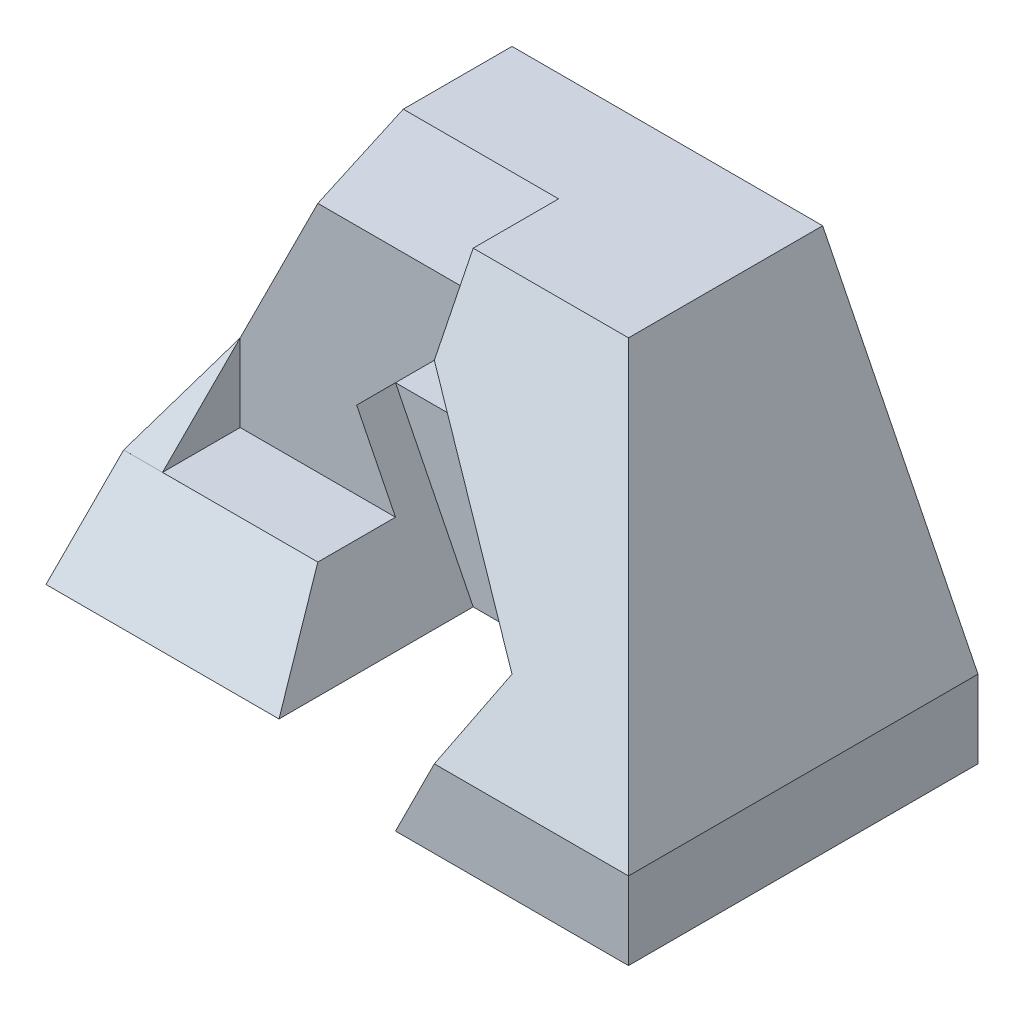
SolidWorks part; units mm, degrees
ref_plane "Front Plane" through (0, 0, 0) normal (0, 0, 1) x (1, 0, 0)
ref_plane "Top Plane" through (0, 0, 0) normal (0, 1, 0) x (1, 0, 0)
ref_plane "Right Plane" through (0, 0, 0) normal (1, 0, 0) x (0, 0, -1)
sketch "Sketch1" plane through (0, 0, 0) normal (0, 0, 1) x (1, 0, 0)
  line L0 (0, 0) -> (0, 20)
  line L1 (0, 20) -> (40, 100)
  line L2 (40, 100) -> (120, 100)
  line L3 (120, 100) -> (160, 20)
  line L4 (160, 20) -> (160, 0)
  line L5 (160, 0) -> (0, 0)
  dimension "D1" = 160
  dimension "D2" = 20
  dimension "D3" = 20
  dimension "D4" = 80
  dimension "D5" = 40
  dimension "D6" = 40
extrude "Boss-Extrude1" add sketch "Sketch1" along normal blind 90
sketch "Sketch2" plane through (0, 0, 0) normal (1, 0, 0) x (0, 0, -1)
  line L0 (0, 100) -> (-50, 100)
  line L1 (-50, 100) -> (-90, 20)
  line L2 (-90, 20) -> (-90, 0)
  line L3 (-90, 0) -> (0, 0)
  line L4 (0, 0) -> (0, 100)
  line L5 (-90, 20) -> (-90, 100)
  line L6 (-90, 100) -> (-50, 100)
  dimension "D1" = 50
  dimension "D2" = 0
extrude "Cut-Extrude1" cut sketch "Sketch2" along normal blind 251 contours L6 L5 L1
ref_plane "Plane1" through (0, 0, 90) normal (0, 0, 1) x (1, 0, 0)
sketch "Sketch7" plane through (0, 0, 90) normal (0, 0, 1) x (1, 0, 0)
  line L0 (60, 0) -> (100, 0)
  line L1 (0, 0) -> (160, 0) construction
  line L2 (100, 0) -> (120, 40)
  line L3 (120, 40) -> (80, 80)
  line L4 (80, 80) -> (40, 40)
  line L5 (40, 40) -> (60, 0)
  dimension "D1" = 40
  dimension "D2" = 60
  dimension "D3" = 20
  dimension "D4" = 20
  dimension "D5" = 40
  dimension "D6" = 40
  dimension "D7" = 20
  dimension "D8" = 40
extrude "Cut-Extrude7" cut sketch "Sketch7" against normal blind 40
sketch "Sketch8" plane through (0, 0, 50) normal (0, 0, 1) x (1, 0, 0)
  line L0 (40, 40) -> (120, 40)
  line L1 (120, 40) -> (80, 80)
  line L2 (80, 80) -> (40, 40)
extrude "Cut-Extrude8" cut sketch "Sketch8" against normal blind 20
sketch "Sketch9" plane through (0, 0, 0) normal (0, 1, 0) x (1, 0, 0)
  line L0 (160, -90) -> (110, -90) construction
  line L1 (40, -80) -> (110, -80)
  line L2 (40, -80) -> (40, -90)
  line L3 (40, -90) -> (110, -90)
  line L4 (110, -80) -> (110, -90)
  dimension "D1" = 10
  dimension "D2" = 70
  dimension "D3" = 50
  dimension "D4" = 0
extrude "Cut-Extrude9" cut sketch "Sketch9" along normal blind 190
sketch "Sketch10" plane through (0, 0, 0) normal (0, -1, 0) x (-1, 0, 0)
  line L0 (0, -90) -> (0, 0) construction
  line L1 (0, -90) -> (-39.999, -90)
  line L2 (0, -90) -> (0, -60.001)
  line L3 (0, -60.001) -> (-39.999, -60.001)
  line L4 (-39.999, -90) -> (-39.999, -60.001)
  line L5 (0, -90) -> (-40, -90) construction
  dimension "D1" = 39.999
  dimension "D2" = 29.999
extrude "Cut-Extrude13" cut sketch "Sketch10" against normal blind 190
sketch "Sketch11" plane through (40, 0, 0) normal (1, 0, 0) x (0, 0, -1)
  line L0 (-80, 40) -> (-80, 0)
  line L1 (-80, 0) -> (-90, 0)
  line L2 (-90, 0) -> (-90, 20)
  line L3 (-90, 20) -> (-80, 40)
extrude "Cut-Extrude14" cut sketch "Sketch11" against normal blind 190
sketch "Sketch12" plane through (0, 0, 0) normal (0, -1, 0) x (-1, 0, 0)
  line L0 (-39.999, -80) -> (-60, -80)
  line L1 (-39.999, -60.001) -> (-39.999, -80) construction
  line L2 (-60, -80) -> (-39.999, -80) construction
  line L3 (-60, -80) -> (-60, -70)
  line L4 (-60, -50) -> (-60, -80) construction
  line L5 (-60, -70) -> (-39.999, -80)
  line L6 (-100, -70) -> (-100, -80)
  line L7 (-80, -60) -> (-120, -80) construction
  line L8 (-100, -80) -> (-110, -80)
  line L9 (-100, -70) -> (-110, -75)
  line L10 (-110, -75) -> (-110, -80)
  line L11 (-100, -70) -> (-110, -75)
  line M9 (-110, -80) -> (-100, -80)
  line M10 (-100, -80) -> (-100, -50)
  dimension "D1" = 10
extrude "Cut-Extrude15" cut sketch "Sketch12" against normal blind 190 contours L9 L10 M9 M10 | L0 L3 L5
sketch "Sketch13" plane through (0, 0, 90) normal (0, 0, 1) x (1, 0, 0)
  line L0 (110, 20) -> (110, 0)
  line L1 (110, 0) -> (100, 0)
  line L2 (100, 0) -> (110, 20)
extrude "Boss-Extrude2" add sketch "Sketch13" against normal blind 34
sketch "Sketch14" plane through (0, 0, 60.001) normal (0, 0, 1) x (1, 0, 0)
  line L1 (0, 20) -> (39.999, 20)
  line L2 (0, 20) -> (0, 0)
  line L3 (0, 0) -> (39.999, 0)
  line L4 (39.999, 20) -> (39.999, 0)
extrude "Boss-Extrude3" add sketch "Sketch14" along normal blind 34
sketch "Sketch15" plane through (0, 0, 94.001) normal (0, 0, 1) x (1, 0, 0)
  line L0 (39.999, 0) -> (60, 0)
  line L1 (60, 0) -> (39.999, 20)
  line L2 (39.999, 20) -> (39.999, 0)
extrude "Boss-Extrude4" add sketch "Sketch15" against normal blind 34
sketch "Sketch17" plane through (0, 0, 50) normal (0, 0, 1) x (1, 0, 0)
  line L0 (40, 40) -> (40, 0)
  line L1 (40, 40) -> (60, 0)
  line L2 (60, 0) -> (40, 0)
  line L3 (40, 40) -> (40, 20)
  line L4 (40, 20) -> (60, 0)
  line L5 (40, 40) -> (60, 0)
  line L6 (40, 40) -> (60, 0)
  line M3 (40, 40) -> (60, 0)
  dimension "D1" = 20
  dimension "D2" = 20
  dimension "D3" = 20
extrude "Cut-Extrude21" cut sketch "Sketch17" along normal blind 77 contours L0 L4 M3
sketch "Sketch21" plane through (40, 0, 0) normal (1, 0, 0) x (0, 0, -1)
  line L0 (-94.001, 20) -> (-94.001, 0) construction
  line L1 (-50, 20) -> (-93.001, 20)
  line L2 (-50, 20) -> (-50, 40)
  line L3 (-50, 40) -> (-93.001, 40)
  line L4 (-93.001, 20) -> (-93.001, 40)
  point P5 (-94.001, 10)
  dimension "D1" = 1
  dimension "D2" = 20
extrude "Cut-Extrude26" cut sketch "Sketch21" against normal blind 77
sketch "Sketch22" plane through (30, 30, 0) normal (0.7071, 0.7071, 0) x (0.7071, -0.7071, 0)
  line L1 (14.1421, -50) -> (42.4264, -50)
  line L2 (14.1421, -50) -> (14.1421, -94.001)
  line L3 (14.1421, -94.001) -> (42.4264, -94.001)
  line L4 (42.4264, -50) -> (42.4264, -94.001)
extrude "Cut-Extrude27" cut sketch "Sketch22" against normal blind 77
sketch "Sketch23" plane through (0, 0, 94.001) normal (0, 0, 1) x (1, 0, 0)
  line L0 (20, 0) -> (49.999, 0)
  line L1 (49.999, 0) -> (39.999, 20)
  line L2 (39.999, 20) -> (39.999, 0)
  line M1 (20, 0) -> (39.9995, 19.9995)
  dimension "D1" = 10
extrude "Boss-Extrude5" add sketch "Sketch23" against normal blind 77 contours L2 L0 L1 M1 | L2 L0 M1
ref_plane "Plane4" through (0, 44.3389, 80.6143) normal (0, -0.4819, -0.8762) x (-1, 0, 0)
sketch "Sketch26" plane through (0, 44.3389, 80.6143) normal (0, -0.4819, -0.8762) x (-1, 0, 0)
  line L0 (-40, 63.5248) -> (-39.999, -27.7774)
  line L1 (-39.999, -27.7774) -> (0, -27.7774)
  line L2 (0, -27.7774) -> (-40, 63.5248)
extrude "Boss-Extrude7" add sketch "Sketch26" along normal blind 50
sketch "Sketch27" plane through (0, 40, 80) normal (0, 0.4472, 0.8944) x (1, 0, 0)
  line L0 (120, 67.082) -> (40, 67.082)
  line L1 (120, 67.082) -> (160, -22.3607)
sketch "Sketch28" plane through (0, 0, 94.001) normal (0, 0, 1) x (1, 0, 0)
  line L0 (0, 0) -> (60, 0)
  line L1 (0, 20) -> (0, 0)
  line L2 (0, 20) -> (50, 20)
  line L3 (50, 20) -> (60, 0)
  dimension "D1" = 60
  dimension "D2" = 50
extrude "Boss-Extrude8" add sketch "Sketch28" against normal blind 50
sketch "Sketch31" plane through (0, 0, 94.001) normal (0, 0, 1) x (1, 0, 0)
  line L0 (50, 20) -> (40.001, 40)
  line L1 (40.001, 40) -> (39.999, 20)
  line L2 (39.999, 20) -> (50, 20)
  dimension "D1" = 20
  dimension "D2" = 9.999
extrude "Boss-Extrude12" add sketch "Sketch31" against normal blind 50
sketch "Sketch32" plane through (48, 24, 0) normal (0.8944, 0.4472, 0) x (0, 0, -1)
  line L0 (-94.001, -26.8328) -> (-94.001, -4.4721) construction
  line L1 (-50, -26.8328) -> (-94.001, -26.8328)
  line L2 (-50, -26.8328) -> (-50, 17.9418)
  line L3 (-50, 17.9418) -> (-94.001, 17.9418)
  line L4 (-94.001, -26.8328) -> (-94.001, 17.9418)
  dimension "D1" = 0
extrude "Cut-Extrude29" cut sketch "Sketch32" along normal blind 2
sketch "Sketch33" plane through (0, 0, 0) normal (0, -1, 0) x (1, 0, 0)
  line L0 (0, 57.6382) -> (2.0482, 47.9374)
  line L1 (2.0482, 47.9374) -> (39.9991, 47.9374)
  line L2 (39.9991, 47.9374) -> (39.999, 57.6382)
  line L3 (39.999, 57.6382) -> (0, 57.6382)
extrude "Cut-Extrude30" cut sketch "Sketch33" along normal blind 26
sketch "Sketch35" plane through (11.6501, 0, 2.4597) normal (0.9784, 0, 0.2066) x (0.2066, 0, -0.9784)
  line L0 (-48.783, -4.0964) -> (-56.3949, 0)
  line L1 (-56.3949, 0) -> (-46.4802, 0)
  line L2 (-46.4802, 0) -> (-48.783, -4.0964)
extrude "Cut-Extrude33" cut sketch "Sketch35" against normal blind 26
ref_plane "Plane5" through (2.0636, 42.2937, 82.5238) normal (0.0222, 0.456, 0.8897) x (0.9998, -0.0101, -0.0198)
sketch "Sketch36" plane through (2.0636, 42.2937, 82.5238) normal (0.0222, 0.456, 0.8897) x (0.9998, -0.0101, -0.0198)
  line L0 (117.9656, 66.1886) -> (37.9656, 66.1886)
  line L1 (117.9656, 66.1886) -> (157.9755, -23.2497)
  line L2 (157.9755, -23.2497) -> (-2.0641, -25.0746)
  line L3 (-2.0641, -25.0746) -> (37.9656, 66.1886)
  dimension "D1" = 80
extrude "Cut-Extrude34" cut sketch "Sketch36" along normal blind 26
sketch "Sketch38" plane through (0, -24.3389, 13.3867) normal (0, -0.8762, 0.4819) x (-1, 0, 0)
  line L0 (0, -42.0033) -> (-1.5725, -42.0033)
  line L1 (-1.5725, -42.0033) -> (0, -50.5032)
  line L2 (0, -50.5032) -> (-1.5725, -42.0033) construction
  line L3 (0, -42.0033) -> (0, -50.5032) construction
  line L4 (0, -50.5032) -> (0, -42.0033)
extrude "Cut-Extrude38" cut sketch "Sketch38" against normal blind 5
sketch "Sketch39" plane through (0, 0, 0) normal (-1, 0, 0) x (0, 0, 1)
  line L0 (47.9374, 0) -> (0, 0) construction
  line L1 (45.8061, 0) -> (63.3168, 0)
  line L2 (45.8061, 0) -> (45.8061, 5.1178)
  line L3 (45.8061, 5.1178) -> (63.3168, 5.1178)
  line L4 (63.3168, 0) -> (63.3168, 5.1178)
  line L5 (94.001, 20) -> (94.001, 0) construction
  dimension "D1" = 17.5107
  dimension "D2" = 5.1178
  dimension "D3" = 48.1949
extrude "Boss-Extrude13" add sketch "Sketch39" against normal blind 5
sketch "Sketch40" plane through (-8, 4, 0) normal (-0.8944, 0.4472, 0) x (0, 0, 1)
  line L0 (60.001, 84.9683) -> (50, 17.8885)
  line L1 (60.001, 84.9683) -> (50, 107.3313) construction
  line L2 (60.001, 40.2492) -> (60.001, 84.9683) construction
  line L3 (50, 17.8885) -> (94.001, 17.8885)
  line L4 (94.001, 17.8885) -> (60.001, 84.9683)
extrude "Boss-Extrude14" add sketch "Sketch40" against normal blind 5
sketch "Sketch41" plane through (-8, 4, 0) normal (-0.8944, 0.4472, 0) x (0, 0, 1)
  line L0 (94.001, 17.8885) -> (50, 17.8885) construction
  line L1 (30.5204, 48.25) -> (66.9463, 48.25)
  line L2 (30.5204, 48.25) -> (30.5204, 17.8885)
  line L3 (30.5204, 17.8885) -> (66.9463, 17.8885)
  line L4 (66.9463, 48.25) -> (66.9463, 17.8885)
  dimension "D1" = 27.0547
  dimension "D2" = 36.4259
  dimension "D3" = 30.3614
extrude "Boss-Extrude17" add sketch "Sketch41" against normal blind 5
sketch "Sketch43" plane through (0, 0, 0) normal (-1, 0, 0) x (0, 0, 1)
  line L0 (94.001, 0) -> (0, 0) construction
  line L1 (94.001, 20) -> (90.001, 20)
  line L2 (94.001, 20) -> (94.001, 0)
  line L3 (94.001, 0) -> (90.001, 0)
  line L4 (90.001, 20) -> (90.001, 0)
  dimension "D1" = 4
extrude "Cut-Extrude39" cut sketch "Sketch43" against normal blind 64
sketch "Sketch44" plane through (0, 20, 0) normal (0, -1, 0) x (1, 0, 0)
  line L1 (0, 90.001) -> (50, 90.001)
  line L2 (0, 90.001) -> (0, 94.001)
  line L3 (0, 94.001) -> (50, 94.001)
  line L4 (50, 90.001) -> (50, 94.001)
extrude "Cut-Extrude40" cut sketch "Sketch44" against normal blind 64
sketch "Sketch45" plane through (0, 40, 80) normal (0, 0.4472, 0.8944) x (1, 0, 0)
  line L1 (120, 67.082) -> (0, 67.082)
  line L2 (120, 67.082) -> (120, -22.3611)
  line L3 (120, -22.3611) -> (0, -22.3611)
  line L4 (0, 67.082) -> (0, -22.3611)
  dimension "D1" = 0
extrude "Cut-Extrude43" cut sketch "Sketch45" along normal blind 64
sketch "Sketch47" plane through (0, 40, 80) normal (0, 0.4472, 0.8944) x (1, 0, 0)
  line L1 (39.9762, 0.0533) -> (62.0895, 0.0533)
  line L2 (39.9762, 0.0533) -> (39.9762, -22.2325)
  line L3 (39.9762, -22.2325) -> (62.0895, -22.2325)
  line L4 (62.0895, 0.0533) -> (62.0895, -22.2325)
extrude "Boss-Extrude19" add sketch "Sketch47" along normal blind 2
sketch "Sketch48" plane through (0, 40, 80) normal (0, 0.4472, 0.8944) x (1, 0, 0)
  line L1 (0, -22.3607) -> (120, -22.3607)
  line L2 (0, -22.3607) -> (0, 67.082)
  line L3 (0, 67.082) -> (120, 67.082)
  line L4 (120, -22.3607) -> (120, 67.082)
extrude "Cut-Extrude44" cut sketch "Sketch48" along normal blind 5
sketch "Sketch49" plane through (0, 40, 80) normal (0, 0.4472, 0.8944) x (1, 0, 0)
  line L0 (40.001, -0.0022) -> (39.999, -22.0916)
  line L1 (39.999, -22.0916) -> (50.0002, -22.3611)
  line L2 (0, -22.3611) -> (50.0002, -22.3611) construction
  line L3 (50.0002, -22.3611) -> (40.001, -0.0022) construction
  line L4 (50.0002, -22.3611) -> (40.001, -0.0022)
extrude "Cut-Extrude47" cut sketch "Sketch49" against normal blind 5
sketch "Sketch52" plane through (0, 0, 50) normal (0, 0, 1) x (1, 0, 0)
  line L0 (40.1191, 40.1191) -> (39.9762, 40.0476)
  line L1 (39.9762, 40.0476) -> (39.9994, 40)
  line L2 (39.9994, 40) -> (40.1191, 40.1191)
extrude "Boss-Extrude24" add sketch "Sketch52" along normal blind 30
sketch "Sketch53" plane through (0, 40, 80) normal (0, 0.4472, 0.8944) x (1, 0, 0)
  line L0 (39.9993, 0.0003) -> (39.999, -22.0916)
  line L1 (39.999, -22.0916) -> (50.0002, -22.3611)
  line L2 (0, -22.3611) -> (50.0002, -22.3611) construction
  line L3 (50.0002, -22.3611) -> (40.001, -0.0022) construction
  line L4 (50.0002, -22.3611) -> (39.9993, 0.0003)
extrude "Boss-Extrude26" add sketch "Sketch53" against normal blind 30
sketch "Sketch56" plane through (-8, 4, 0) normal (-0.8944, 0.4472, 0) x (0, 0, 1)
  line L1 (40.3762, 47.4163) -> (72.6753, 47.4163)
  line L2 (40.3762, 47.4163) -> (40.3762, 20.1968)
  line L3 (40.3762, 20.1968) -> (72.6753, 20.1968)
  line L4 (72.6753, 47.4163) -> (72.6753, 20.1968)
extrude "Boss-Extrude27" add sketch "Sketch56" against normal blind 30
sketch "Sketch57" plane through (48, 24, 0) normal (0.8944, 0.4472, 0) x (0, 0, -1)
  line L0 (-90.001, -26.8328) -> (-90.001, -4.4721) construction
  line L1 (-50, 17.889) -> (-90.001, 17.889)
  line L2 (-50, 17.889) -> (-50, -7.698)
  line L3 (-50, -7.698) -> (-90.001, -7.698)
  line L4 (-90.001, 17.889) -> (-90.001, -7.698)
extrude "Boss-Extrude28" add sketch "Sketch57" against normal blind 30
sketch "Sketch61" plane through (0, 40, 80) normal (0, 0.4472, 0.8944) x (1, 0, 0)
  line L0 (0, -22.3607) -> (29.999, 44.7191) construction
  line L1 (10, 0) -> (58.9154, 0)
  line L2 (10, 0) -> (10, -22.3611)
  line L3 (10, -22.3611) -> (58.9154, -22.3611)
  line L4 (58.9154, 0) -> (58.9154, -22.3611)
  line L5 (0, -22.3611) -> (16.4592, -22.3611) construction
  dimension "D1" = 0
  dimension "D2" = 22.3611
extrude "Cut-Extrude55" cut sketch "Sketch61" along normal blind 20
sketch "Sketch62" plane through (0, 0, 30) normal (0, 0, 1) x (1, 0, 0)
  line L0 (80, 80) -> (40, 40)
  line L1 (40, 40) -> (120, 40)
  line L2 (120, 40) -> (80, 80) construction
  line L3 (40, 40) -> (120, 40) construction
  line L4 (120, 40) -> (80, 80)
extrude "Boss-Extrude30" add sketch "Sketch62" along normal blind 10
ref_plane "Plane6" through (0, 0, 40) normal (0, 0, 1) x (1, 0, 0)
sketch "Sketch63" plane through (0, 0, 40) normal (0, 0, 1) x (1, 0, 0)
  line L0 (80, 80) -> (40, 40)
  line L1 (40, 40) -> (0, 20)
  line L2 (80, 80) -> (80, 100)
  line L3 (80, 100) -> (40, 100)
  line L4 (40, 100) -> (0, 20)
  line L5 (120, 100) -> (40, 100) construction
  line L6 (0, 20) -> (50, 20)
  line L7 (50, 20) -> (40, 40)
  dimension "D1" = 0
extrude "Cut-Extrude56" cut sketch "Sketch63" along normal blind 79 contours L3 L4 L1 L0 L2 | L6 L7 L1
sketch "Sketch64" plane through (0, 0, 0) normal (1, 0, 0) x (0, 0, -1)
  line L0 (-60, 80) -> (-40, 80)
  line L1 (-60, 80) -> (-50, 100)
  line L2 (-50, 100) -> (-28, 100)
  line L3 (-28, 100) -> (-40, 80)
  line L4 (-40, 100) -> (0, 100) construction
  line L5 (-60, 80) -> (-50, 100) construction
  dimension "D1" = 0
  dimension "D2" = 20
  dimension "D3" = 22
extrude "Cut-Extrude57" cut sketch "Sketch64" along normal blind 79
sketch "Sketch65" plane through (80, 0, 0) normal (-1, 0, 0) x (0, 0, 1)
  line L0 (40, 100) -> (28, 100)
  line L1 (28, 100) -> (40, 80)
  line L2 (40, 80) -> (40, 100)
extrude "Cut-Extrude58" cut sketch "Sketch65" along normal blind 79
sketch "Sketch66" plane through (0, 0, 50) normal (0, 0, 1) x (1, 0, 0)
  line L0 (40, 40) -> (120, 40)
  line L1 (120, 40) -> (100, 0)
  line L2 (100, 0) -> (60, 0)
  line L3 (60, 0) -> (40, 40)
extrude "Cut-Extrude59" cut sketch "Sketch66" against normal blind 10
sketch "Sketch67" plane through (0, 0, 0) normal (1, 0, 0) x (0, 0, -1)
  line L0 (-90.001, 0) -> (-90.001, 20)
  line L1 (-90.001, 20) -> (-80, 40.002)
  line L2 (-40, 40.002) -> (-80, 40.002)
  line L3 (-40, 40.002) -> (-80.001, 0)
  line L4 (-90.001, 0) -> (0, 0) construction
  line L5 (-80.001, 0) -> (-90.001, 0)
  line L6 (-80, 40) -> (-90, 20) construction
  line L8 (-40, 40.002) -> (-40, 20)
  line L9 (-40, 20) -> (-60.0005, 20.001)
  dimension "D1" = 10
  dimension "D2" = 20
extrude "Cut-Extrude64" cut sketch "Sketch67" along normal blind 20 contours L5 L3 L2 L1 L0
sketch "Sketch71" plane through (0, 0, 0) normal (-1, 0, 0) x (0, 0, 1)
  line L0 (60.0015, 20) -> (40, 40)
  line L1 (40, 40) -> (40, 20)
  line L2 (60.0015, 20) -> (40, 20) construction
  line L3 (40, 20) -> (60.0015, 20)
  dimension "D1" = 0
extrude "Boss-Extrude32" add sketch "Sketch71" against normal blind 20
sketch "Sketch72" plane through (20, 0, 0) normal (-1, 0, 0) x (0, 0, 1)
  line L0 (60.0015, 20) -> (80.001, 0)
  line L1 (80.001, 0) -> (90.001, 0)
  line L2 (90.001, 0) -> (90, 20)
  line L3 (90, 20) -> (60.0015, 20)
extrude "Cut-Extrude65" cut sketch "Sketch72" against normal blind 49
sketch "Sketch73" plane through (0, 0.0045, 90.001) normal (0, 0, -1) x (-1, 0, 0)
  line L1 (-20, 19.9955) -> (-78.5189, 19.9955)
  line L2 (-20, 19.9955) -> (-20, -4.9993)
  line L3 (-20, -4.9993) -> (-78.5189, -4.9993)
  line L4 (-78.5189, 19.9955) -> (-78.5189, -4.9993)
extrude "Cut-Extrude66" cut sketch "Sketch73" against normal blind 49
sketch "Sketch75" plane through (0, 40.0005, 40.0015) normal (0, 0.7071, 0.7071) x (1, 0, 0)
  line L0 (60, -56.5685) -> (0, -56.5685) construction
  line L1 (20, -56.5685) -> (0, -56.5685)
  line L2 (20, -56.5685) -> (20, 0)
  line L3 (20, 0) -> (0, 0)
  line L4 (0, -56.5685) -> (0, 0)
  dimension "D1" = 20
extrude "Boss-Extrude33" add sketch "Sketch75" against normal blind 2
sketch "Sketch77" plane through (0, 0, 0) normal (-1, 0, 0) x (0, 0, 1)
  line L0 (77.1726, 0) -> (80.001, 0)
  line L1 (80.001, 0) -> (78.5868, -1.4142)
  line L2 (78.5868, -1.4142) -> (77.1726, 0)
extrude "Cut-Extrude69" cut sketch "Sketch77" against normal blind 29
sketch "Sketch78" plane through (0, 0, 40) normal (0, 0, -1) x (-1, 0, 0)
  line L0 (0, 20) -> (-8.5868, 37.1735)
  line L1 (-8.5868, 37.1735) -> (0, 37.1735)
  line L2 (0, 37.1735) -> (0, 20)
extrude "Cut-Extrude70" cut sketch "Sketch78" against normal blind 29
sketch "Sketch80" plane through (0, 38.5863, 38.5873) normal (0, -0.7071, -0.7071) x (-1, 0, 0)
  line L0 (-9.2932, 0) -> (0, 0)
  line L1 (0, 0) -> (0, -1.9979)
  line L2 (0, -1.9979) -> (-8.5868, -1.9979)
  line L3 (0, -1.9979) -> (-8.5868, -1.9979) construction
  line L4 (-9.2932, 0) -> (-8.5868, -1.9979) construction
  line L5 (-8.5868, -1.9979) -> (-9.2932, 0)
extrude "Cut-Extrude72" cut sketch "Sketch80" against normal blind 2
sketch "Sketch81" plane through (0, 37.1735, 0) normal (0, -1, 0) x (1, 0, 0)
  line L1 (8.5868, 40) -> (0, 40)
  line L2 (8.5868, 40) -> (8.5868, 42.8284)
  line L3 (8.5868, 42.8284) -> (0, 42.8284)
  line L4 (0, 40) -> (0, 42.8284)
extrude "Cut-Extrude73" cut sketch "Sketch81" against normal blind 2
sketch "Sketch82" plane through (-8, 4, 0) normal (-0.8944, 0.4472, 0) x (0, 0, 1)
  line L1 (24.0858, 51.8113) -> (53.3139, 51.8113)
  line L2 (24.0858, 51.8113) -> (24.0858, 30.2169)
  line L3 (24.0858, 30.2169) -> (53.3139, 30.2169)
  line L4 (53.3139, 51.8113) -> (53.3139, 30.2169)
extrude "Cut-Extrude76" cut sketch "Sketch82" along normal blind 40
sketch "Sketch83" plane through (0, 0, 0) normal (-1, 0, 0) x (0, 0, 1)
  line L0 (60.0015, 20) -> (60.0015, 0)
  line L1 (80.001, 0) -> (0, 0) construction
  line L2 (60.0015, 0) -> (80.001, 0)
  line L3 (80.001, 0) -> (60.0015, 20)
extrude "Cut-Extrude77" cut sketch "Sketch83" against normal blind 20
sketch "Sketch86" plane through (0, 0, 40) normal (0, 0, 1) x (1, 0, 0)
  line L0 (80, 80) -> (120, 40)
  line L1 (120, 40) -> (40, 40)
  line L2 (40, 40) -> (80, 80)
  dimension "D1" = 80
extrude "Cut-Extrude82" cut sketch "Sketch86" against normal blind 40
sketch "Sketch87" plane through (0, 0, 0) normal (1, 0, 0) x (0, 0, -1)
  line L0 (0, 20) -> (-25, 20)
  line L2 (-60.0015, 20) -> (0, 20) construction
  line L3 (0, 100) -> (0, 20)
  line L4 (-25, 20) -> (0, 100)
  dimension "D1" = 25
extrude "Cut-Extrude84" cut sketch "Sketch87" along normal blind 39.999
sketch "Sketch89" plane through (39.999, 0, 0) normal (-1, 0, 0) x (0, 0, 1)
  line L0 (0, 20) -> (25, 20)
  line L1 (25, 20) -> (0, 20) construction
  line L2 (25, 20) -> (0, 99.998)
  line L3 (0, 99.998) -> (0, 20)
extrude "Cut-Extrude85" cut sketch "Sketch89" against normal blind 0.0001
sketch "Sketch90" plane through (39.9991, 0, 0) normal (-1, 0, 0) x (0, 0, 1)
  line L0 (25, 20) -> (0, 99.998)
  line L1 (25, 20) -> (0, 99.998) construction
  line L2 (0, 99.998) -> (0, 20) construction
  line L3 (0, 99.998) -> (0, 20)
  line L4 (0, 20) -> (25, 20)
extrude "Boss-Extrude34" add sketch "Sketch90" along normal blind 2
sketch "Sketch91" plane through (37.9991, 0, 0) normal (-1, 0, 0) x (0, 0, 1)
  line L0 (0, 99.998) -> (0, 20)
  line L1 (0, 20) -> (25, 20)
  line L2 (25, 20) -> (0, 99.998) construction
  line L3 (25, 20) -> (0, 99.998)
extrude "Cut-Extrude86" cut sketch "Sketch91" against normal blind 2
sketch "Sketch95" plane through (0, 0, 0) normal (0, 0, -1) x (-1, 0, 0)
  line L0 (-80, 80) -> (-80, 100)
  line L1 (-120, 100) -> (-40, 100) construction
  line L2 (-80, 100) -> (-39.9991, 100)
  line L3 (-39.9991, 99.998) -> (-39.9991, 20) construction
  line L4 (-39.9991, 100) -> (0, 20)
  line L5 (0, 20) -> (-50, 20)
  line L6 (-39.9991, 20) -> (-40, 40)
  line L7 (-40, 40) -> (-80, 80)
  line L8 (-40, 40) -> (-60, 0)
  line L9 (0, 0) -> (-160, 0) construction
  line M1 (-39.9991, 99.998) -> (-39.999, 99.998)
  line M2 (-39.999, 99.998) -> (-40, 100)
  line M3 (-40, 100) -> (-120, 100)
  line M8 (0, 20) -> (-39.9991, 20)
  line M9 (-39.9991, 20) -> (-39.9991, 99.998)
  line M10 (-80, 80) -> (-40, 40)
  dimension "D1" = 40.0009
extrude "Cut-Extrude88" cut sketch "Sketch95" against normal blind 56 contours L6 L0 M9 M1 M2 M3 M10 | L6 L8 L5 | L4 L2 M2 M1 M9 M8
sketch "Sketch96" plane through (0, 0, 40) normal (0, 0, 1) x (1, 0, 0)
  line L0 (40, 40) -> (120, 40)
  line L1 (120, 40) -> (100, 0)
  line L2 (100, 0) -> (60, 0)
  line L3 (60, 0) -> (40, 40)
extrude "Boss-Extrude40" add sketch "Sketch96" along normal blind 20
sketch "Sketch97" plane through (0, 0, 56) normal (0, 0, -1) x (-1, 0, 0)
  line L0 (-20, 24.0016) -> (-2.0008, 24.0016)
  line L1 (-2.0008, 24.0016) -> (0, 20)
  line L2 (0, 20) -> (-20, 20)
  line L3 (0, 20) -> (-20, 20) construction
  line L4 (-20, 20) -> (-20, 24.0016)
extrude "Cut-Extrude89" cut sketch "Sketch97" against normal blind 20
sketch "Sketch98" plane through (0, 0, 0) normal (0, 0, -1) x (-1, 0, 0)
  line L0 (-80, 80) -> (-120, 40)
  line L1 (-120, 40) -> (-40, 40)
  line L2 (-40, 40) -> (-80, 80)
extrude "Boss-Extrude41" add sketch "Sketch98" against normal blind 50
sketch "Sketch99" plane through (0, 0, 0) normal (0, 0, -1) x (-1, 0, 0)
  line L0 (-50, 20) -> (0, 20)
  line L1 (0, 20) -> (-40, 100)
  line L2 (-40, 100) -> (-80, 100)
  line L3 (-80, 100) -> (-80, 80)
  line L4 (-80, 80) -> (-40, 40)
  line L5 (-40, 40) -> (-50, 20)
  line L6 (-50, 20) -> (0, 20)
  line L7 (-120, 100) -> (-80, 100) construction
  line M1 (-40, 40) -> (-80, 80)
  line M2 (-80, 80) -> (-80, 100)
  line M8 (0, 20) -> (-50, 20)
  line M9 (-50, 20) -> (-40, 40)
extrude "Boss-Extrude42" add sketch "Sketch99" against normal blind 40 contours L1 L2 M2 M1 M9 M8
sketch "Sketch100" plane through (20, 0, 0) normal (-1, 0, 0) x (0, 0, 1)
  line L0 (60.0015, 20) -> (60.0015, 0)
  line L1 (60.0015, 0) -> (80.001, 0)
  line L2 (80.001, 0) -> (60.0015, 20)
extrude "Boss-Extrude43" add sketch "Sketch100" along normal blind 20
sketch "Sketch102" plane through (0, 0, 0) normal (-1, 0, 0) x (0, 0, 1)
  line L1 (0, 0) -> (60.0015, 0)
  line L2 (0, 0) -> (0, 20)
  line L3 (0, 20) -> (60.0015, 20)
  line L4 (60.0015, 0) -> (60.0015, 20)
extrude "Cut-Extrude90" cut sketch "Sketch102" against normal blind 20
sketch "Sketch103" plane through (0, 0, 0) normal (0, 0, -1) x (-1, 0, 0)
  line L0 (0, 20) -> (-20, 0)
  line L1 (-20, 0) -> (-20, 20)
  line L2 (-20, 20) -> (0, 20)
extrude "Boss-Extrude44" add sketch "Sketch103" against normal blind 60
ref_plane "Plane9" through (80, 0, 0) normal (1, 0, 0) x (0, 0, -1)
sketch "Sketch105" plane through (80, 0, 0) normal (1, 0, 0) x (0, 0, -1)
  line L0 (-60, 80) -> (-40, 80)
  line L1 (-40, 80) -> (-28, 100)
  line L2 (-28, 100) -> (-50, 100)
  line L3 (-50, 100) -> (-60, 80)
  dimension "D1" = 20
  dimension "D2" = 22
  dimension "D3" = 20
extrude "Cut-Extrude91" cut sketch "Sketch105" against normal blind 60
sketch "Sketch106" plane through (80, 0, 0) normal (-1, 0, 0) x (0, 0, 1)
  line L0 (60, 80) -> (40, 80)
  line L1 (40, 80) -> (40, 40)
  line L2 (40, 40) -> (80, 40)
  line L3 (80, 40) -> (60, 80)
  dimension "D1" = 40
  dimension "D2" = 0
extrude "Cut-Extrude92" cut sketch "Sketch106" along normal blind 60
sketch "Sketch107" plane through (0, 0, 50) normal (0, 0, 1) x (1, 0, 0)
  line L0 (120, 40) -> (80, 40)
  line L1 (80, 40) -> (80, 80)
  line L2 (80, 80) -> (120, 40) construction
  line L3 (80, 40) -> (80, 80) construction
  line L4 (80, 80) -> (120, 40)
extrude "Cut-Extrude93" cut sketch "Sketch107" against normal blind 10
sketch "Sketch109" plane through (0, 0, 60) normal (0, 0, 1) x (1, 0, 0)
  line L0 (50, 20) -> (50, 40)
  line L1 (120, 40) -> (40, 40) construction
  line L2 (50, 40) -> (40, 40)
  line L3 (40, 40) -> (50, 20)
extrude "Cut-Extrude96" cut sketch "Sketch109" against normal blind 20
sketch "Sketch111" plane through (0, 0, 60) normal (0, 0, 1) x (1, 0, 0)
  line L0 (120, 40) -> (50, 40)
  line L1 (50, 40) -> (50, 20)
  line L2 (50, 20) -> (60, 0)
  line L3 (60, 0) -> (100, 0)
  line L4 (100, 0) -> (120, 40)
extrude "Cut-Extrude98" cut sketch "Sketch111" against normal blind 20
sketch "Sketch112" plane through (0, 0, 0) normal (1, 0, 0) x (0, 0, -1)
  line L0 (-60, 20) -> (-40, 39.9995)
  line L1 (-40, 39.9995) -> (-40, 20)
  line L2 (-40, 20) -> (-60, 20)
  line L3 (-80.001, 0) -> (-60.0015, 20) construction
extrude "Boss-Extrude45" add sketch "Sketch112" along normal blind 20
sketch "Sketch113" plane through (0, 0, 40) normal (0, 0, -1) x (-1, 0, 0)
  line L0 (-9.9998, 39.9995) -> (0, 39.9995)
  line L1 (0, 39.9995) -> (0, 20)
  line L2 (0, 20) -> (-9.9998, 39.9995)
extrude "Cut-Extrude99" cut sketch "Sketch113" against normal blind 20
sketch "Sketch114" plane through (20, 0, 0) normal (1, 0, 0) x (0, 0, -1)
  line L0 (-40, 39.9995) -> (-60.0015, 20)
  line L1 (-60.0015, 20) -> (-40, 20)
  line L2 (-40, 20) -> (-40, 39.9995)
extrude "Cut-Extrude100" cut sketch "Sketch114" against normal blind 10
sketch "Sketch115" plane through (0, 0, 40) normal (0, 0, 1) x (1, 0, 0)
  line L0 (80, 80) -> (120, 40)
  line L1 (120, 40) -> (40, 40)
  line L2 (40, 40) -> (80, 80)
  dimension "D1" = 80
extrude "Cut-Extrude101" cut sketch "Sketch115" against normal blind 142
ref_plane "Plane11" through (0, 23.4497, 58.6215) normal (0, -0.3714, -0.9285) x (-1, 0, 0)
sketch "Sketch117" plane through (0, 0, 0) normal (1, 0, 0) x (0, 0, -1)
  line L0 (0, 20) -> (-25, 20)
  line L1 (-60, 20) -> (0, 20) construction
  line L2 (-25, 20) -> (0, 100)
  line L3 (0, 100) -> (0, 20)
  line L4 (-28, 100) -> (0, 100) construction
  dimension "D1" = 25
  dimension "D2" = 0
extrude "Cut-Extrude106" cut sketch "Sketch117" along normal blind 39.999
sketch "Sketch118" plane through (0, 0, 40) normal (0, 0, 1) x (1, 0, 0)
  line L0 (40, 40) -> (120, 40)
  line L1 (120, 40) -> (100, 0)
  line L2 (100, 0) -> (60, 0)
  line L3 (60, 0) -> (40, 40)
extrude "Cut-Extrude107" cut sketch "Sketch118" against normal blind 10
